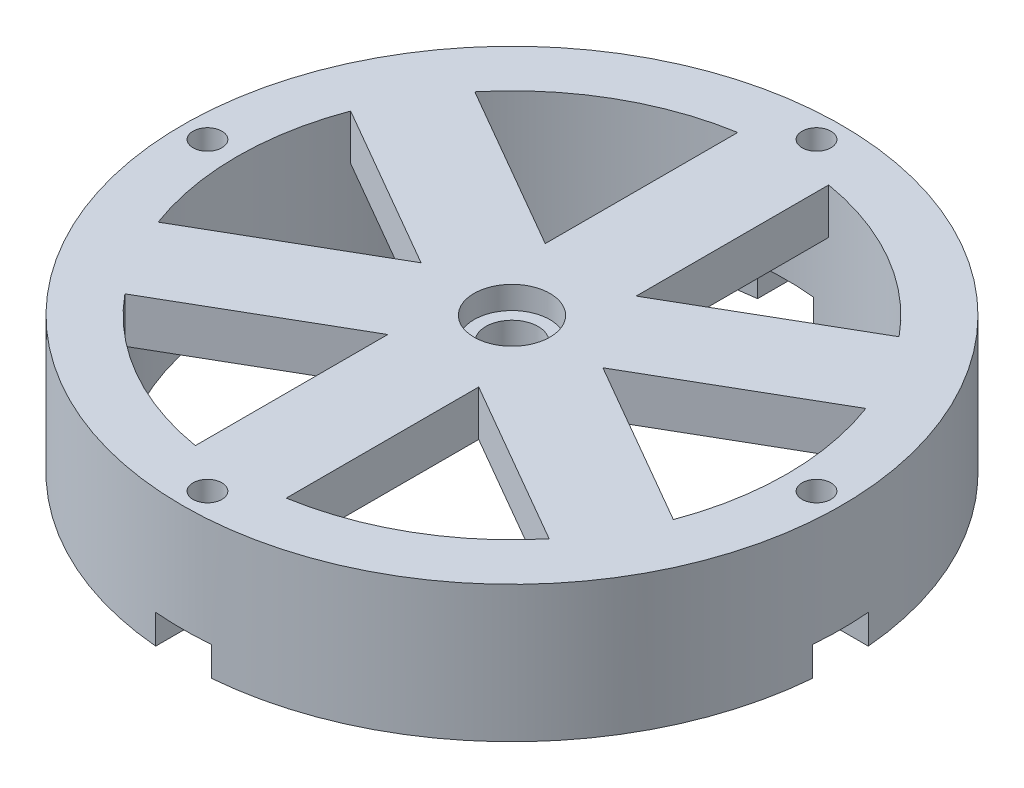
SolidWorks part; units mm, degrees
ref_plane "Front Plane" through (0, 0, 0) normal (0, 0, 1) x (1, 0, 0)
ref_plane "Top Plane" through (0, 0, 0) normal (0, 1, 0) x (1, 0, 0)
ref_plane "Right Plane" through (0, 0, 0) normal (1, 0, 0) x (0, 0, -1)
sketch "Sketch1" plane through (0, 0, 0) normal (0, 1, 0) x (1, 0, 0)
  line L24 (10, 17.3205) -> (10, 59.6678)
  line L34 (10, 17.3205) -> (46.6739, 38.4942)
  line L36 (-10, 17.3205) -> (-10, 59.6678)
  line L37 (-10, 17.3205) -> (-46.6739, 38.4942)
  line L38 (-20, 0) -> (-56.6739, 21.1737)
  line L39 (-20, 0) -> (-56.6739, -21.1737)
  line L40 (-10, -17.3205) -> (-46.6739, -38.4942)
  line L41 (-10, -17.3205) -> (-10, -59.6678)
  line L42 (10, -17.3205) -> (10, -59.6678)
  line L43 (10, -17.3205) -> (46.6739, -38.4942)
  line L44 (20, 0) -> (56.6739, 21.1737)
  line L45 (20, 0) -> (56.6739, -21.1737)
  circle A3 centre (0, 67) radius 3.175
  circle A13 centre (67, 0) radius 3.175
  circle A14 centre (0, -67) radius 3.175
  circle A15 centre (-67, 0) radius 3.175
  arc A16 (46.6739, 38.4942) -> (10, 59.6678) centre (0, 0) ccw
  arc A17 (-10, 59.6678) -> (-46.6739, 38.4942) centre (0, 0) ccw
  arc A18 (-56.6739, 21.1737) -> (-56.6739, -21.1737) centre (0, 0) ccw
  arc A19 (-46.6739, -38.4942) -> (-10, -59.6678) centre (0, 0) ccw
  arc A20 (10, -59.6678) -> (46.6739, -38.4942) centre (0, 0) ccw
  arc A21 (56.6739, -21.1737) -> (56.6739, 21.1737) centre (0, 0) ccw
  circle A23 centre (0, 0) radius 72.5
  point P24 (0, 0)
  point P35 (0, 0)
  point P46 (0, 0)
  point P68 (0, 0)
  dimension "D1" = 145
  dimension "D2" = 4
  dimension "D6" = 6.35
extrude "Boss-Extrude1" add sketch "Sketch1" along normal blind 10
sketch "Sketch8" plane through (0, 10, 0) normal (0, 1, 0) x (1, 0, 0)
  circle A0 centre (0, 0) radius 8.35
  dimension "D1" = 16.7
extrude "Cut-Extrude4" cut sketch "Sketch8" against normal blind 5
sketch "Sketch9" plane through (0, 10, 0) normal (0, 1, 0) x (1, 0, 0)
  circle A0 centre (0, 0) radius 5.75
  dimension "D1" = 11.5
extrude "Cut-Extrude5" cut sketch "Sketch9" against normal through all both and the other way through all
sketch "Sketch10" plane through (0, 0, 0) normal (0, -1, 0) x (1, 0, 0)
  circle A0 centre (0, 0) radius 60.5
  circle A1 centre (0, 0) radius 72.5
  circle A3 centre (0, -67) radius 3.175
  circle A4 centre (-67, 0) radius 3.175
  circle A5 centre (0, 67) radius 3.175
  circle A6 centre (67, 0) radius 3.175
  point P16 (0, 0)
  dimension "D2" = 145
  dimension "D1" = 4
extrude "Boss-Extrude4" add sketch "Sketch10" along normal blind 20
sketch "Sketch11" plane through (0, -20, 0) normal (0, -1, 0) x (1, 0, 0)
  line L0 (0, 0) -> (0, -60.5)
  line L1 (-44.3636, -6.15) -> (-44.3636, 6.15)
  line L2 (6.15, -44.3636) -> (-6.15, -44.3636)
  line L3 (6.15, -44.3636) -> (6.15, -76.6364)
  line L4 (6.15, -76.6364) -> (-6.15, -76.6364)
  line L5 (-6.15, -44.3636) -> (-6.15, -76.6364)
  line L6 (6.15, -44.3636) -> (-6.15, -76.6364) construction
  line L7 (6.15, -76.6364) -> (-6.15, -44.3636) construction
  line L8 (-44.3636, -6.15) -> (-76.6364, -6.15)
  line L9 (-76.6364, -6.15) -> (-76.6364, 6.15)
  line L10 (-44.3636, 6.15) -> (-76.6364, 6.15)
  line L11 (-44.3636, -6.15) -> (-76.6364, 6.15) construction
  line L12 (-76.6364, -6.15) -> (-44.3636, 6.15) construction
  line L13 (0, 0) -> (-60.5, 0)
  line L14 (-6.15, 44.3636) -> (6.15, 44.3636)
  line L15 (-6.15, 44.3636) -> (-6.15, 76.6364)
  line L16 (-6.15, 76.6364) -> (6.15, 76.6364)
  line L17 (6.15, 44.3636) -> (6.15, 76.6364)
  line L18 (-6.15, 44.3636) -> (6.15, 76.6364) construction
  line L19 (-6.15, 76.6364) -> (6.15, 44.3636) construction
  line L20 (0, 0) -> (0, 60.5)
  line L21 (44.3636, 6.15) -> (44.3636, -6.15)
  line L22 (44.3636, 6.15) -> (76.6364, 6.15)
  line L23 (76.6364, 6.15) -> (76.6364, -6.15)
  line L24 (44.3636, -6.15) -> (76.6364, -6.15)
  line L25 (44.3636, 6.15) -> (76.6364, -6.15) construction
  line L26 (76.6364, 6.15) -> (44.3636, -6.15) construction
  line L27 (0, 0) -> (60.5, 0)
  circle A0 centre (0, 0) radius 60.5 construction
  point P28 (0, 0)
  dimension "D1" = 12.3
  dimension "D2" = 4
extrude "Cut-Extrude6" cut sketch "Sketch11" against normal blind 6.45 contours L3 L4 L5 L2 | L10 L9 L8 L1 | L17 L16 L15 L14 | L22 L23 L24 L21
sketch "Sketch12" plane through (0, -20, 0) normal (0, -1, 0) x (1, 0, 0)
  line L0 (0, 0) -> (0, 67)
  line L1 (0, 0) -> (33.5, 58.0237)
  line L2 (0, 0) -> (58.0237, 33.5)
  line L3 (0, 0) -> (67, 0)
  circle A0 centre (0, 0) radius 67
  circle A1 centre (33.5, 58.0237) radius 2.15
  circle A2 centre (58.0237, 33.5) radius 2.15
  circle A3 centre (33.5, -58.0237) radius 2.15
  circle A4 centre (58.0237, -33.5) radius 2.15
  circle A5 centre (-58.0237, -33.5) radius 2.15
  circle A6 centre (-33.5, -58.0237) radius 2.15
  circle A7 centre (-33.5, 58.0237) radius 2.15
  circle A8 centre (-58.0237, 33.5) radius 2.15
  point P25 (0, 0)
  dimension "D3" = 4.3
  dimension "D4" = 4.3
  dimension "D5" = 4
  dimension "D1" = 30
  dimension "D2" = 30
extrude "Cut-Extrude7" cut sketch "Sketch12" against normal blind 6 contours A8 | A7 | A1 | A2 | A4 | A3 | A6 | A5
